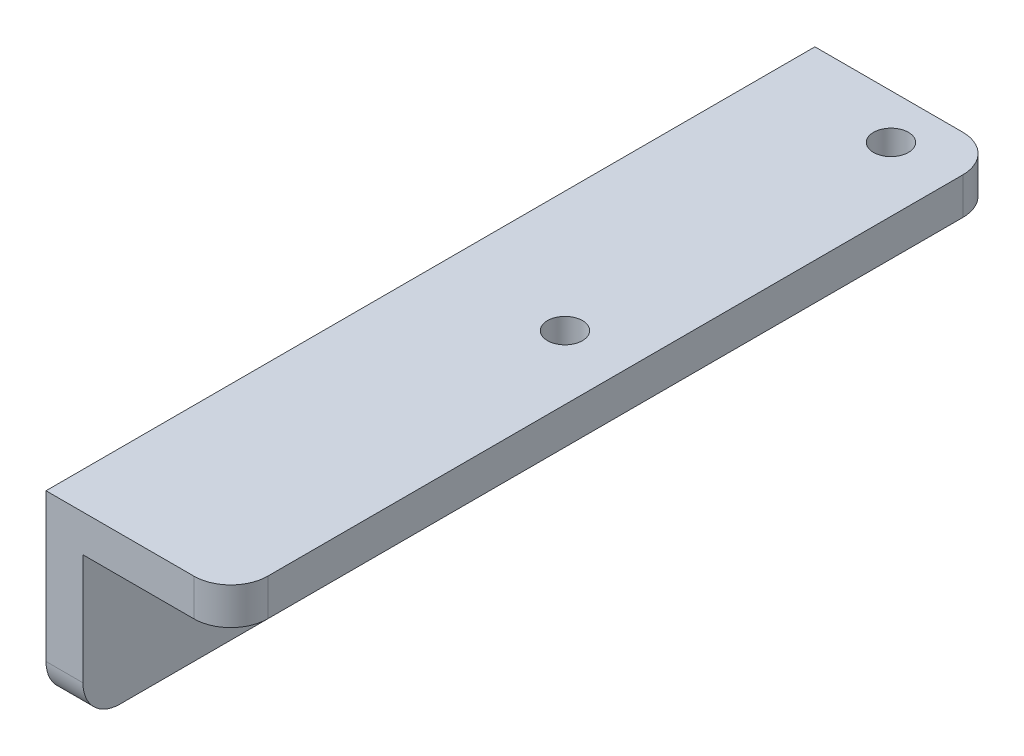
SolidWorks part; units mm, degrees
ref_plane "Front Plane" through (0, 0, 0) normal (0, 0, 1) x (1, 0, 0)
ref_plane "Top Plane" through (0, 0, 0) normal (0, 1, 0) x (1, 0, 0)
ref_plane "Right Plane" through (0, 0, 0) normal (1, 0, 0) x (0, 0, -1)
sketch "Sketch1" plane through (0, 0, 0) normal (0, 0, 1) x (1, 0, 0)
  line L0 (0, 0) -> (0, -15.875)
  line L1 (0, 0) -> (15.875, 0)
  line L3 (0, -15.875) -> (3.175, -15.875)
  line L4 (3.175, -15.875) -> (3.175, -3.175)
  line L5 (3.175, -3.175) -> (15.875, -3.175)
  line L6 (15.875, -3.175) -> (15.875, 0)
  dimension "D1" = 15.875
  dimension "D2" = 3.175
extrude "Boss-Extrude1" add sketch "Sketch1" against normal blind 66.04 contours L5 L6 L1 L0 L3 L4
sketch "Sketch2" plane through (3.175, 0, 0) normal (1, 0, 0) x (0, 0, -1)
  line L0 (66.04, 0) -> (0, 0) construction
  line L1 (0, -15.875) -> (0, -3.175) construction
  circle A2 centre (29.95, -9.525) radius 2.5
  circle A3 centre (9.95, -9.525) radius 2.5
  dimension "D2" = 5
  dimension "D1" = 20
  dimension "D3" = 9.525
  dimension "D4" = 9.95
extrude "Cut-Extrude1" cut sketch "Sketch2" against normal through all
ref_plane "Plane1" through (0, 0, -19.685) normal (0, 0, 1) x (1, 0, 0)
sketch "Sketch3" plane through (0, 0, -19.685) normal (0, 0, 1) x (1, 0, 0)
  line L0 (3.175, -15.875) -> (3.175, -3.175) construction
  line L1 (3.175, -3.175) -> (15.875, -3.175) construction
  line L2 (3.175, -15.875) -> (3.175, -3.175)
  line L3 (3.175, -3.175) -> (15.875, -3.175)
  line L4 (3.175, -15.875) -> (15.875, -3.175)
extrude "Boss-Extrude2" add sketch "Sketch3" along normal mid plane 5.08
sketch "Sketch4" plane through (0, 0, -66.04) normal (0, 0, -1) x (-1, 0, 0)
  line L0 (-3.175, -15.875) -> (-3.175, -3.175) construction
  line L1 (0, -15.875) -> (-3.175, -15.875)
  line L2 (0, -15.875) -> (0, -8.255)
  line L3 (0, -8.255) -> (-3.175, -8.255)
  line L4 (-3.175, -15.875) -> (-3.175, -8.255)
  dimension "D1" = 7.62
extrude "Cut-Extrude2" cut sketch "Sketch4" against normal blind 25.4
sketch "Sketch5" plane through (0, -3.175, 0) normal (0, -1, 0) x (1, 0, 0)
  circle A0 centre (10.375, -34.1967) radius 1.5 construction
  circle A1 centre (10.375, -62.1967) radius 1.5 construction
  circle A2 centre (10.375, -34.1967) radius 1.5
  circle A3 centre (10.375, -62.1967) radius 1.5
extrude "Cut-Extrude3" cut sketch "Sketch5" against normal blind 25.4
fillet "Fillet1" radius 3.175 5 edges at (15.875, -1.5875, 0) (1.5875, -15.875, 0) (15.875, -1.5875, -66.04) (1.5875, -8.255, -66.04) (1.5875, -15.875, -40.64)
